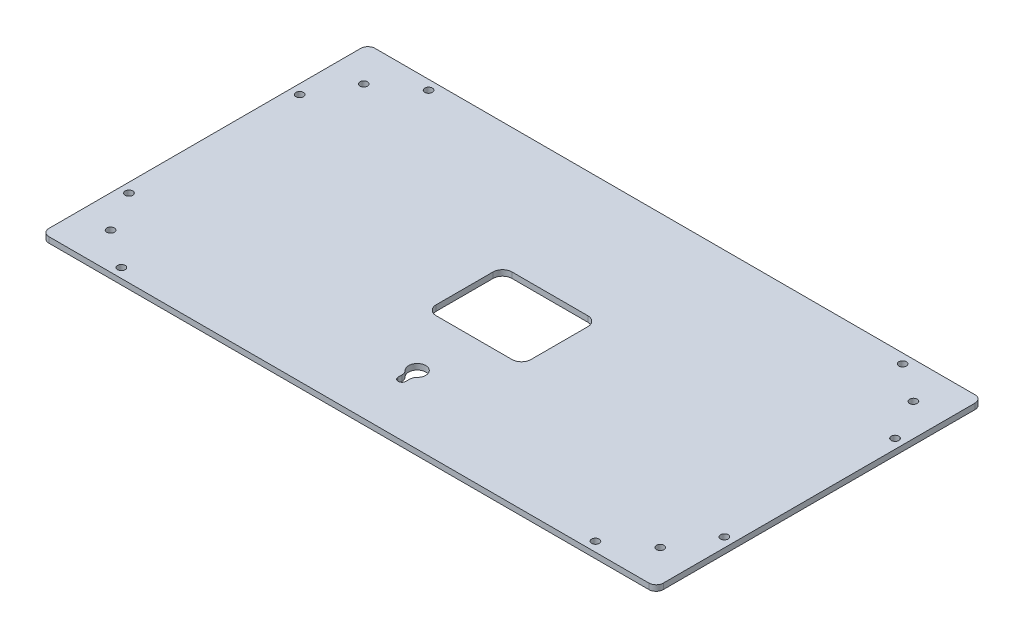
SolidWorks part; units mm, degrees
ref_plane "前视基准面" through (0, 0, 0) normal (0, 0, 1) x (1, 0, 0)
ref_plane "上视基准面" through (0, 0, 0) normal (0, 1, 0) x (1, 0, 0)
ref_plane "右视基准面" through (0, 0, 0) normal (1, 0, 0) x (0, 0, -1)
ref_plane "基准面1" through (0, -3, 0) normal (0, -1, 0) x (1, 0, 0)
sketch "草图1" plane through (0, -3, 0) normal (0, -1, 0) x (1, 0, 0)
  line L0 (2, 58) -> (2, 56)
  line L1 (-2, 56) -> (-2, 58)
  line L2 (162, -82.2) -> (162, 82.2)
  line L3 (158.2, 86) -> (-158.2, 86)
  line L4 (-162, 82.2) -> (-162, -82.2)
  line L5 (-158.2, -86) -> (158.2, -86)
  line L6 (25, 15) -> (25, -15)
  line L7 (20, -20) -> (-20, -20)
  line L8 (-25, -15) -> (-25, 15)
  line L9 (-20, 20) -> (20, 20)
  circle A0 centre (-144.95, 66.75) radius 2
  circle A1 centre (-144.95, -66.75) radius 2
  circle A2 centre (144.95, -66.75) radius 2
  circle A3 centre (144.95, 66.75) radius 2
  arc A4 (-2, 58) -> (2, 58) centre (0, 58) cw
  arc A5 (2, 56) -> (3.1765, 53.1667) centre (6, 56) ccw
  arc A6 (3.1765, 53.1667) -> (-3.1765, 53.1667) centre (0, 49.9792) cw
  arc A7 (-3.1765, 53.1667) -> (-2, 56) centre (-6, 56) ccw
  circle A8 centre (157, 45) radius 2
  circle A9 centre (157, -45) radius 2
  circle A10 centre (125, -81) radius 2
  circle A11 centre (-125, -81) radius 2
  circle A12 centre (-157, -45) radius 2
  circle A13 centre (-157, 45) radius 2
  circle A14 centre (125, 81) radius 2
  circle A15 centre (-125, 81) radius 2
  arc A16 (162, 82.2) -> (158.2, 86) centre (158.2, 82.2) ccw
  arc A17 (-158.2, 86) -> (-162, 82.2) centre (-158.2, 82.2) ccw
  arc A18 (-162, -82.2) -> (-158.2, -86) centre (-158.2, -82.2) ccw
  arc A19 (158.2, -86) -> (162, -82.2) centre (158.2, -82.2) ccw
  arc A20 (20, 20) -> (25, 15) centre (20, 15) cw
  arc A21 (25, -15) -> (20, -20) centre (20, -15) cw
  arc A22 (-20, -20) -> (-25, -15) centre (-20, -15) cw
  arc A23 (-25, 15) -> (-20, 20) centre (-20, 15) cw
extrude "凸台-拉伸1" add sketch "草图1" against normal blind 3
